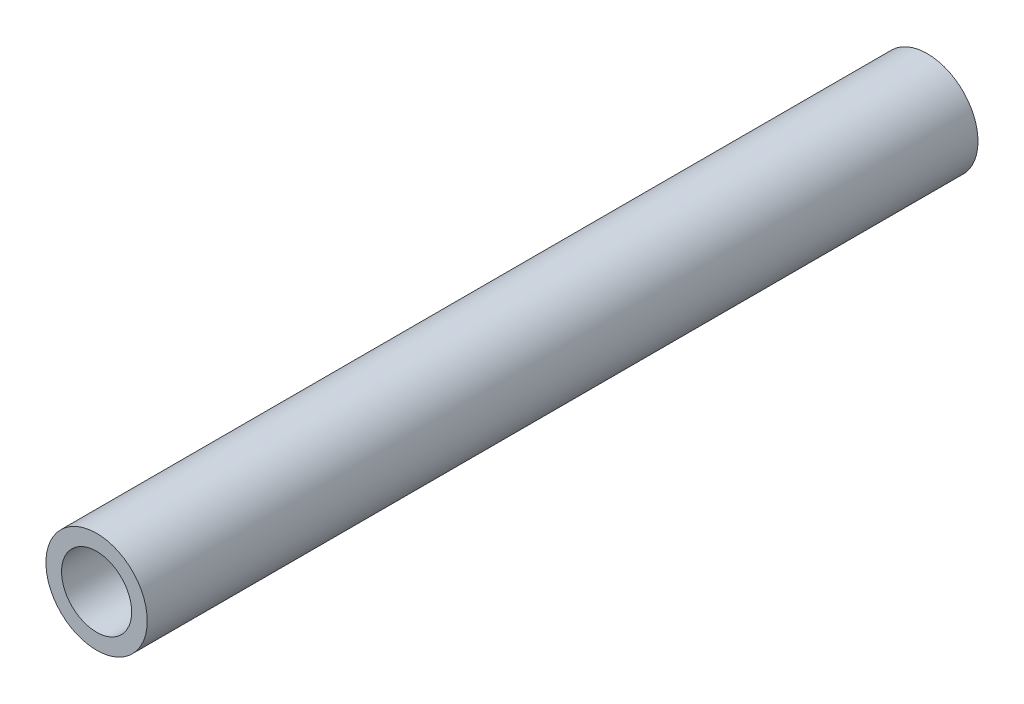
SolidWorks part; units mm, degrees
material "PVC Rigid"
ref_plane "Front Plane" through (0, 0, 0) normal (0, 0, 1) x (1, 0, 0)
ref_plane "Top Plane" through (0, 0, 0) normal (0, 1, 0) x (1, 0, 0)
ref_plane "Right Plane" through (0, 0, 0) normal (1, 0, 0) x (0, 0, -1)
sketch "Sketch1" plane through (0, 0, 0) normal (0, 0, 1) x (1, 0, 0)
  circle A0 centre (0, 0) radius 7.747
  circle A1 centre (0, 0) radius 5.3594
  dimension "D1" = 15.494
  dimension "D2" = 10.7188
extrude "Boss-Extrude1" add sketch "Sketch1" along normal blind 127
